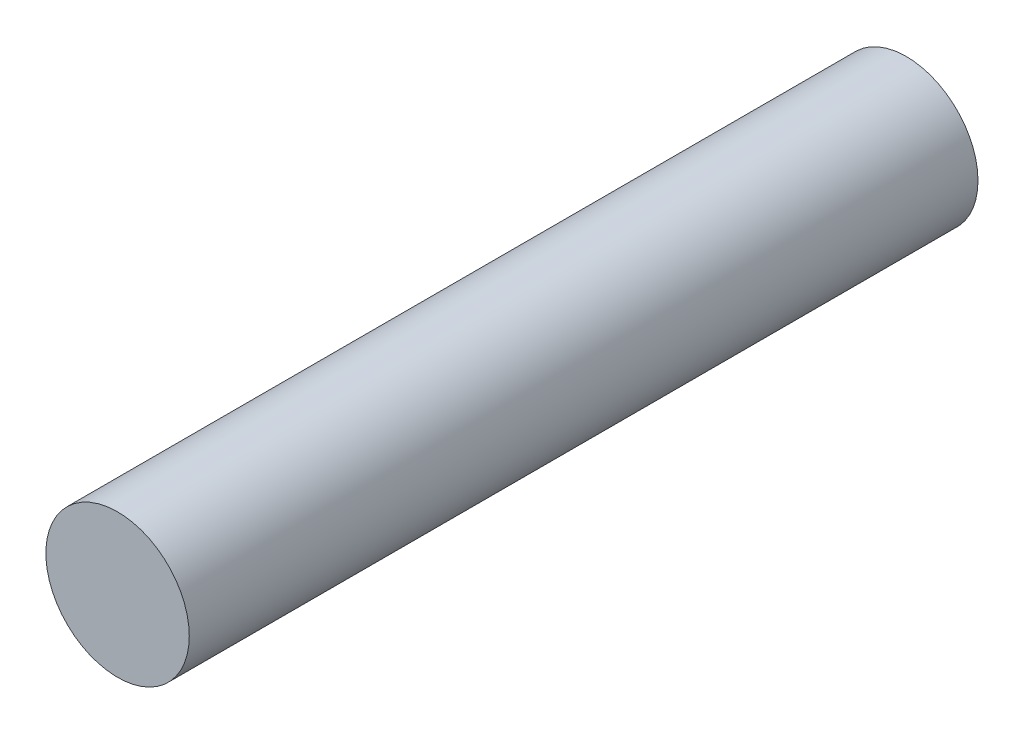
SolidWorks part; units mm, degrees
ref_plane "Front Plane" through (0, 0, 0) normal (0, 0, 1) x (1, 0, 0)
ref_plane "Top Plane" through (0, 0, 0) normal (0, 1, 0) x (1, 0, 0)
ref_plane "Right Plane" through (0, 0, 0) normal (1, 0, 0) x (0, 0, -1)
sketch "Sketch1" plane through (0, 0, 0) normal (0, 0, 1) x (1, 0, 0)
  circle A0 centre (0, 0) radius 3.175
  dimension "D1" = 6.35
extrude "Boss-Extrude1" add sketch "Sketch1" along normal blind 34.925 contours A0
